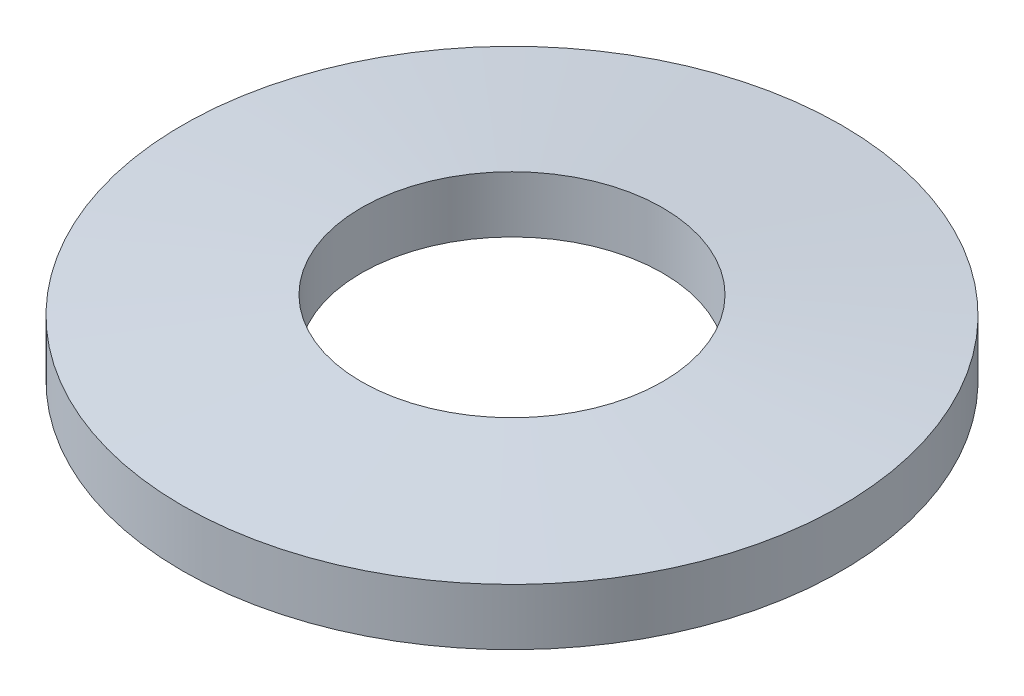
SolidWorks part; units mm, degrees
ref_plane "Front Plane" through (0, 0, 0) normal (0, 0, 1) x (1, 0, 0)
ref_plane "Top Plane" through (0, 0, 0) normal (0, 1, 0) x (1, 0, 0)
ref_plane "Right Plane" through (0, 0, 0) normal (1, 0, 0) x (0, 0, -1)
sketch "Sketch1" plane through (0, 0, 0) normal (0, 0, 1) x (1, 0, 0)
  line L0 (0, 0) -> (0, 38.5251) construction
  line L1 (1.6, 0.79) -> (1.6, 0.19)
  line L2 (1.6, 0.19) -> (3.5, 0)
  line L3 (3.5, 0) -> (3.5, 0.6)
  line L4 (3.5, 0.6) -> (1.6, 0.79)
  dimension "D1" = 3.2
  dimension "D2" = 7
  dimension "D3" = 0.79
  dimension "D4" = 0.6
revolve "Revolve1" add sketch "Sketch1" angle 360 about L0
